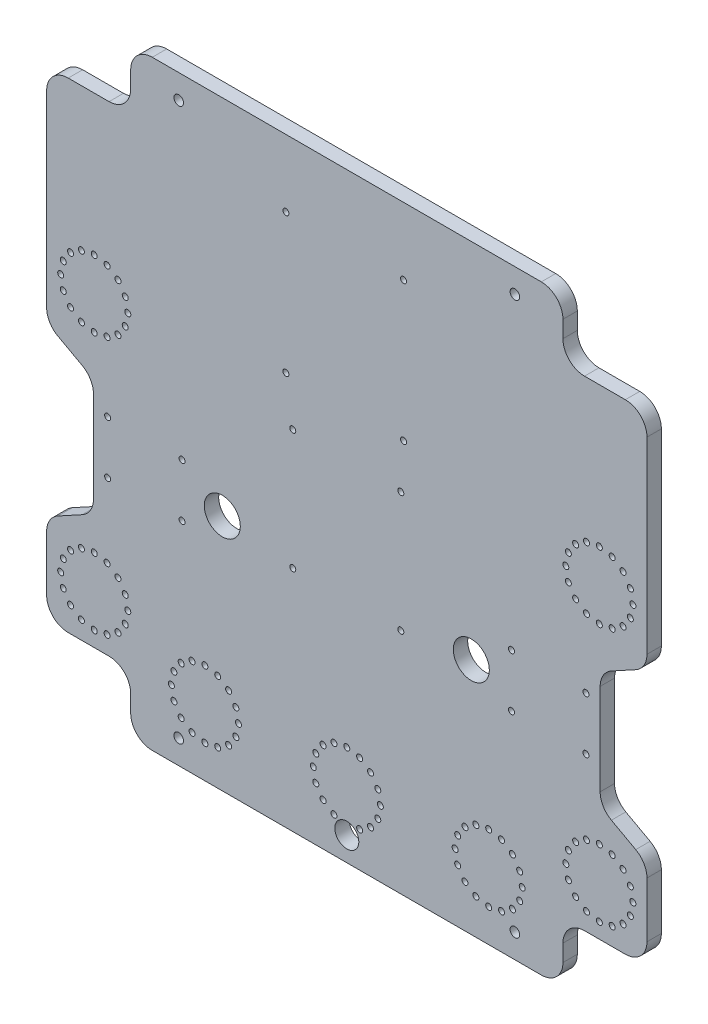
SolidWorks part; units mm, degrees
other "Markup1"
sketch "Sketch7" plane through (25, 0, 0) normal (-0.133, -0.1918, 0.9724) x (0.9904, 0.0125, 0.1379)
material "6061 Alloy"
ref_plane "Front Plane" through (0, 0, 0) normal (0, 0, 1) x (1, 0, 0)
ref_plane "Top Plane" through (0, 0, 0) normal (0, 1, 0) x (1, 0, 0)
ref_plane "Right Plane" through (0, 0, 0) normal (1, 0, 0) x (0, 0, -1)
sketch "Sketch1" plane through (0, 0, 0) normal (0, 0, 1) x (1, 0, 0)
  line L1 (0, 0) -> (300, 0)
  line L2 (0, 0) -> (0, 250)
  line L3 (0, 250) -> (300, 250)
  line L4 (300, 0) -> (300, 250)
  dimension "D1" = 300
  dimension "D2" = 250
extrude "Boss-Extrude1" add sketch "Sketch1" against normal blind 6
sketch "Motor Center Line" plane through (0, 0, -6) normal (0, 0, -1) x (-1, 0, 0)
  line L0 (0, 100) -> (-300, 100) construction
  line L3 (-300, 250) -> (0, 250) construction
  dimension "D1" = 150
sketch "Sketch2" plane through (0, 0, 0) normal (0, 0, 1) x (1, 0, 0)
  line L0 (150, 0.825) -> (150, -0.825) construction
  line L1 (0, 0) -> (20, 0)
  line L2 (0, 0) -> (0, 20)
  line L3 (0, 20) -> (20, 20)
  line L4 (20, 0) -> (20, 20)
  line L5 (300, 20) -> (280, 20)
  line L6 (280, 0) -> (280, 20)
  line L7 (300, 0) -> (280, 0)
  line L8 (300, 0) -> (300, 20)
  line L10 (0, 125) -> (300, 125) construction
  line L11 (0, 250) -> (0, 0) construction
  line L12 (300, 0) -> (300, 250) construction
  line L13 (300, 250) -> (300, 230)
  line L14 (300, 250) -> (280, 250)
  line L15 (280, 250) -> (280, 230)
  line L16 (300, 230) -> (280, 230)
  line L17 (0, 230) -> (20, 230)
  line L18 (20, 250) -> (20, 230)
  line L19 (0, 250) -> (20, 250)
  line L20 (0, 250) -> (0, 230)
  dimension "D1" = 20
sketch "Sketch3" plane through (0, 0, 0) normal (0, 0, 1) x (1, 0, 0)
  line L0 (150, 250) -> (150, 0) construction
  line L1 (0, 0) -> (25, 0)
  line L2 (0, 0) -> (0, 25)
  line L3 (0, 25) -> (25, 25)
  line L4 (25, 0) -> (25, 25)
  line L5 (300, 250) -> (0, 250) construction
  line L6 (0, 0) -> (300, 0) construction
  line L7 (0, 125) -> (300, 125) construction
  line L8 (0, 250) -> (0, 0) construction
  line L9 (300, 0) -> (300, 250) construction
  line L10 (300, 25) -> (275, 25)
  line L11 (275, 0) -> (275, 25)
  line L12 (300, 0) -> (275, 0)
  line L13 (300, 0) -> (300, 25)
  line L14 (300, 250) -> (300, 225)
  line L15 (300, 250) -> (275, 250)
  line L16 (275, 250) -> (275, 225)
  line L17 (300, 225) -> (275, 225)
  line L18 (0, 225) -> (25, 225)
  line L19 (25, 250) -> (25, 225)
  line L20 (0, 250) -> (25, 250)
  line L21 (0, 250) -> (0, 225)
  line L22 (255.5, 73) -> (275, 62.3437)
  line L23 (255.5, 73) -> (255.5, 121.6874)
  line L24 (255.5, 121.6874) -> (275, 132.3437)
  line L25 (275, 132.3437) -> (300, 132.3437)
  line L26 (300, 132.3437) -> (300, 25)
  line L27 (275, 62.3437) -> (275, 25)
  line L28 (44.5, 73) -> (25, 62.3437)
  line L29 (25, 62.3437) -> (25, 25)
  line L30 (44.5, 73) -> (44.5, 121.6874)
  line L31 (265.5, 121.25) -> (265.5, 78.75) construction
  line L32 (44.5, 121.6874) -> (25, 132.3437)
  line L37 (287.5, 132.3437) -> (287.5, 225)
  line L38 (25, 132.3437) -> (0, 132.3437)
  line L39 (12.5, 132.3437) -> (12.5, 225)
  circle A0 centre (201.85, 99.1258) radius 7.5
  circle A1 centre (98.15, 99.1258) radius 7.5
  ellipse E4 centre (201.85, 99.7743) end of major axis (201.2, 99.7743) minor radius 0.6484 construction
  dimension "D3" = 15
  dimension "D1" = 25
  dimension "D2" = 10
  dimension "D4" = 70
extrude "Cut-Extrude1" cut sketch "Sketch3" against normal through all both and the other way through all
sketch "Sketch8" plane through (0, 0, 0) normal (0, 0, 1) x (1, 0, 0)
  circle A0 centre (209.09, 27.66) radius 13.97 construction
  circle A25 centre (209.09, 41.63) radius 1.25
  circle A26 centre (209.09, 13.69) radius 1.25
  circle A27 centre (214.4361, 40.5666) radius 1.25
  circle A28 centre (203.7439, 14.7534) radius 1.25
  circle A29 centre (218.9683, 37.5383) radius 1.25
  circle A30 centre (199.2117, 17.7817) radius 1.25
  circle A31 centre (221.9966, 33.0061) radius 1.25
  circle A32 centre (196.1834, 22.3139) radius 1.25
  circle A33 centre (223.06, 27.66) radius 1.25
  circle A34 centre (195.12, 27.66) radius 1.25
  circle A35 centre (221.9966, 22.3139) radius 1.25
  circle A36 centre (196.1834, 33.0061) radius 1.25
  circle A37 centre (218.9683, 17.7817) radius 1.25
  circle A38 centre (199.2117, 37.5383) radius 1.25
  circle A39 centre (214.4361, 14.7534) radius 1.25
  circle A40 centre (203.7439, 40.5666) radius 1.25
  circle A43 centre (195.12, 27.66) radius 1.6 construction
  circle A44 centre (223.06, 27.66) radius 1.6 construction
  circle A45 centre (90.91, 27.66) radius 13.97 construction
  circle A46 centre (76.94, 27.66) radius 1.25
  circle A47 centre (104.88, 27.66) radius 1.25
  circle A48 centre (76.94, 27.66) radius 1.6 construction
  circle A49 centre (255.1689, 59.2712) radius 1.25
  circle A50 centre (103.8166, 22.3139) radius 1.25
  circle A51 centre (78.0034, 33.0061) radius 1.25
  circle A52 centre (100.7883, 17.7817) radius 1.25
  circle A53 centre (81.0317, 37.5383) radius 1.25
  circle A54 centre (96.2561, 14.7534) radius 1.25
  circle A55 centre (85.5639, 40.5666) radius 1.25
  circle A56 centre (90.91, 13.69) radius 1.25
  circle A57 centre (90.91, 41.63) radius 1.25
  circle A58 centre (85.5639, 14.7534) radius 1.25
  circle A59 centre (96.2561, 40.5666) radius 1.25
  circle A60 centre (81.0317, 17.7817) radius 1.25
  circle A61 centre (100.7883, 37.5383) radius 1.25
  circle A62 centre (78.0034, 22.3139) radius 1.25
  circle A63 centre (103.8166, 33.0061) radius 1.25
  circle A66 centre (104.88, 27.66) radius 1.5 construction
  circle A67 centre (255.1689, 45.3012) radius 13.97 construction
  circle A68 centre (255.1689, 31.3312) radius 1.25
  circle A69 centre (255.1689, 59.2712) radius 1.6 construction
  circle A70 centre (44.8311, 45.3012) radius 13.97 construction
  circle A71 centre (260.515, 58.2078) radius 1.25
  circle A72 centre (249.8228, 32.3946) radius 1.25
  circle A73 centre (265.0472, 55.1795) radius 1.25
  circle A74 centre (245.2907, 35.4229) radius 1.25
  circle A75 centre (268.0755, 50.6473) radius 1.25
  circle A76 centre (242.2623, 39.9551) radius 1.25
  circle A77 centre (269.1389, 45.3012) radius 1.25
  circle A78 centre (241.1989, 45.3012) radius 1.25
  circle A79 centre (268.0755, 39.9551) radius 1.25
  circle A80 centre (242.2623, 50.6473) radius 1.25
  circle A81 centre (265.0472, 35.4229) radius 1.25
  circle A82 centre (245.2907, 55.1795) radius 1.25
  circle A83 centre (260.515, 32.3946) radius 1.25
  circle A84 centre (249.8228, 58.2078) radius 1.25
  circle A87 centre (44.8311, 59.2712) radius 1.25
  circle A88 centre (44.8311, 31.3312) radius 1.25
  circle A89 centre (50.1772, 58.2078) radius 1.25
  circle A90 centre (39.485, 32.3946) radius 1.25
  circle A91 centre (54.7093, 55.1795) radius 1.25
  circle A92 centre (34.9528, 35.4229) radius 1.25
  circle A93 centre (57.7377, 50.6473) radius 1.25
  circle A94 centre (31.9245, 39.9551) radius 1.25
  circle A95 centre (58.8011, 45.3012) radius 1.25
  circle A96 centre (30.8611, 45.3012) radius 1.25
  circle A97 centre (57.7377, 39.9551) radius 1.25
  circle A98 centre (31.9245, 50.6473) radius 1.25
  circle A99 centre (54.7093, 35.4229) radius 1.25
  circle A100 centre (34.9528, 55.1795) radius 1.25
  circle A101 centre (50.1772, 32.3946) radius 1.25
  circle A102 centre (39.485, 58.2078) radius 1.25
  circle A105 centre (44.8311, 31.3312) radius 1.5 construction
  circle A106 centre (44.8311, 59.2712) radius 1.5 construction
  circle A107 centre (255.1689, 152.6711) radius 13.97 construction
  circle A108 centre (255.1689, 166.6411) radius 1.25
  circle A109 centre (255.1689, 138.7011) radius 1.25
  circle A110 centre (249.8228, 139.7645) radius 1.25
  circle A111 centre (260.515, 165.5777) radius 1.25
  circle A112 centre (245.2907, 142.7929) radius 1.25
  circle A113 centre (265.0472, 162.5494) radius 1.25
  circle A114 centre (242.2623, 147.3251) radius 1.25
  circle A115 centre (268.0755, 158.0172) radius 1.25
  circle A116 centre (241.1989, 152.6711) radius 1.25
  circle A117 centre (269.1389, 152.6711) radius 1.25
  circle A118 centre (242.2623, 158.0172) radius 1.25
  circle A119 centre (268.0755, 147.3251) radius 1.25
  circle A120 centre (245.2907, 162.5494) radius 1.25
  circle A121 centre (265.0472, 142.7929) radius 1.25
  circle A122 centre (249.8228, 165.5777) radius 1.25
  circle A123 centre (260.515, 139.7645) radius 1.25
  circle A124 centre (255.1689, 166.6411) radius 1.6 construction
  circle A125 centre (255.1689, 138.7011) radius 1.5 construction
  circle A128 centre (44.8311, 152.6711) radius 13.97 construction
  circle A129 centre (44.8311, 166.6411) radius 1.25
  circle A130 centre (44.8311, 138.7011) radius 1.25
  circle A131 centre (39.485, 139.7645) radius 1.25
  circle A132 centre (50.1772, 165.5777) radius 1.25
  circle A133 centre (34.9528, 142.7929) radius 1.25
  circle A134 centre (54.7093, 162.5494) radius 1.25
  circle A135 centre (31.9245, 147.3251) radius 1.25
  circle A136 centre (57.7377, 158.0172) radius 1.25
  circle A137 centre (30.8611, 152.6711) radius 1.25
  circle A138 centre (58.8011, 152.6711) radius 1.25
  circle A139 centre (31.9245, 158.0172) radius 1.25
  circle A140 centre (57.7377, 147.3251) radius 1.25
  circle A141 centre (34.9528, 162.5494) radius 1.25
  circle A142 centre (54.7093, 142.7929) radius 1.25
  circle A143 centre (39.485, 165.5777) radius 1.25
  circle A144 centre (50.1772, 139.7645) radius 1.25
  circle A147 centre (44.8311, 166.6411) radius 1.6 construction
  circle A148 centre (44.8311, 138.7011) radius 1.6 construction
  circle A149 centre (150, 27.66) radius 13.97 construction
  circle A150 centre (150, 41.63) radius 1.25
  circle A151 centre (150, 13.69) radius 1.25
  circle A152 centre (155.3461, 40.5666) radius 1.25
  circle A153 centre (144.6539, 14.7534) radius 1.25
  circle A154 centre (159.8783, 37.5383) radius 1.25
  circle A155 centre (140.1217, 17.7817) radius 1.25
  circle A156 centre (162.9066, 33.0061) radius 1.25
  circle A157 centre (137.0934, 22.3139) radius 1.25
  circle A158 centre (163.97, 27.66) radius 1.25
  circle A159 centre (136.03, 27.66) radius 1.25
  circle A160 centre (162.9066, 22.3139) radius 1.25
  circle A161 centre (137.0934, 33.0061) radius 1.25
  circle A162 centre (159.8783, 17.7817) radius 1.25
  circle A163 centre (140.1217, 37.5383) radius 1.25
  circle A164 centre (155.3461, 14.7534) radius 1.25
  circle A165 centre (144.6539, 40.5666) radius 1.25
  circle A170 centre (136.03, 27.66) radius 1.6 construction
  circle A171 centre (163.97, 27.66) radius 1.5 construction
  point P40 (209.09, 27.66)
  point P87 (90.91, 27.66)
  point P129 (255.1689, 45.3012)
  point P167 (44.8311, 45.3012)
  point P192 (255.1689, 152.6711)
  point P234 (44.8311, 152.6711)
  point P273 (150, 27.66)
  dimension "D1" = 2.5
  dimension "D2" = 2.5
  dimension "D5" = 2.5
  dimension "D7" = 2.5
  dimension "D9" = 5.4508
  dimension "D10" = 5.3461
  dimension "D11" = 5.3461
  dimension "D12" = 2.5
  dimension "D15" = 2.5
  dimension "D18" = 2.5
  dimension "D20" = 5.4508
  dimension "D14" = 5.4508
  dimension "D17" = 5.4508
  dimension "D3" = 8
  dimension "D4" = 8
  dimension "D6" = 8
  dimension "D8" = 8
  dimension "D13" = 8
  dimension "D16" = 8
  dimension "D19" = 8
sketch "Sketch4" plane through (0, 0, 0) normal (0, 0, 1) x (1, 0, 0)
  arc A0 (174.9953, 164.0221) -> (172.2953, 164.0221) centre (173.6453, 164.0221) ccw construction
  arc A1 (125.9953, 164.0221) -> (123.2953, 164.0221) centre (124.6453, 164.0221) ccw construction
  arc A4 (125.9953, 222.0221) -> (123.2953, 222.0221) centre (124.6453, 222.0221) ccw construction
  arc A5 (174.9953, 222.0221) -> (172.2953, 222.0221) centre (173.6453, 222.0221) ccw construction
  point P23 (127.5, 95)
  point P25 (172.5, 95)
  point P27 (127.5, 145)
  point P29 (172.5, 145)
  point P31 (124.6453, 164.0221)
  point P33 (173.6453, 164.0221)
  point P35 (124.6453, 222.0221)
  point P37 (173.6453, 222.0221)
  point P39 (218.6, 111)
  point P41 (249.6, 111)
  point P43 (249.6, 89)
  point P45 (218.6, 89)
  point P47 (81.4, 89.0063)
  point P49 (50.4, 89.0063)
  point P51 (81.4, 111.0063)
  point P53 (50.4, 111.0063)
extrude "Ultrasonics" cut sketch "Sketch8" against normal through all
sketch "Sketch6" plane through (0, 0, 0) normal (0, 0, 1) x (1, 0, 0)
  line L0 (287.5, 225) -> (275, 225)
  line L1 (275, 0) -> (240, 0)
  line L2 (275, 0) -> (275, 25)
  line L3 (275, 25) -> (240, 25)
  line L4 (240, 0) -> (240, 25)
  line L5 (240, 25) -> (255.5, 73)
  line L6 (150, 250) -> (150, 0) construction
  line L7 (275, 250) -> (25, 250) construction
  line L8 (25, 0) -> (275, 0) construction
  line L9 (60, 25) -> (44.5, 73)
  line L10 (25, 25) -> (60, 25)
  line L11 (60, 0) -> (60, 25)
  line L12 (25, 0) -> (60, 0)
  line L13 (25, 0) -> (25, 25)
  line L14 (275, 250) -> (240, 250)
  line L15 (25, 225) -> (60, 225)
  line L16 (25, 225) -> (25, 250)
  line L17 (25, 250) -> (60, 250)
  line L18 (60, 225) -> (60, 250)
  line L19 (240, 225) -> (240, 250)
  line L20 (275, 225) -> (240, 225)
  line L21 (275, 225) -> (275, 250)
  line L22 (25, 225) -> (25, 132.3437)
  line L23 (275, 132.3437) -> (275, 225)
  line L24 (287.5, 225) -> (287.5, 132.3437)
  line L25 (287.5, 132.3437) -> (275, 132.3437)
  line L26 (25, 225) -> (12.5, 225)
  line L27 (12.5, 225) -> (12.5, 132.3437)
  line L28 (12.5, 132.3437) -> (25, 132.3437)
  dimension "D1" = 25
  dimension "D2" = 35
extrude "Cut-Extrude3" cut sketch "Sketch6" against normal through all
sketch "Sketch5" plane through (0, 0, 0) normal (0, 0, 1) x (1, 0, 0)
  circle A0 centre (50.4, 89.0063) radius 1.25
  dimension "D1" = 2.5
extrude "Cut-Extrude2" cut sketch "Sketch5" against normal through all both
pattern_sketch "Motor Mounts" of "Cut-Extrude2" driven by "Sketch4"
fillet "Fillet1" radius 9 20 edges at (255.5, 121.6874, -3) (44.5, 121.6874, -3) (44.5, 73, -3) (25, 62.3437, -3) (255.5, 73, -3) (275, 62.3437, -3) (240, 250, -3) (240, 225, -3) (60, 250, -3) (60, 225, -3) (60, 0, -3) (240, 0, -3) (275, 225, -3) (275, 132.3437, -3) (25, 225, -3) (25, 132.3437, -3) (60, 25, -3) (25, 25, -3) (275, 25, -3) (240, 25, -3)
sketch "Sketch9" plane through (0, 0, 0) normal (0, 0, 1) x (1, 0, 0)
  line L0 (69, 0) -> (231, 0) construction
  circle A0 centre (150, 10) radius 5
  point P4 (150, 0)
  dimension "D2" = 10
  dimension "D1" = 10
extrude "Limit Switch mount" cut sketch "Sketch9" against normal through all
sketch "Sketch10" plane through (0, 0, 0) normal (0, 0, 1) x (1, 0, 0)
  line L0 (60, 240) -> (240, 240) construction
  line L1 (60, 234) -> (60, 241) construction
  line L2 (240, 234) -> (240, 241) construction
  line L3 (231, 250) -> (69, 250) construction
  line L4 (60, 10) -> (240, 10) construction
  line L5 (60, 9) -> (60, 16) construction
  line L6 (240, 9) -> (240, 16) construction
  line L7 (69, 0) -> (231, 0) construction
  circle A0 centre (80, 240) radius 2
  circle A1 centre (220, 240) radius 2
  circle A2 centre (80, 10) radius 2
  circle A3 centre (220, 10) radius 2
  dimension "D3" = 4
  dimension "D1" = 10
  dimension "D2" = 10
  dimension "D4" = 20
  dimension "D5" = 20
  dimension "D6" = 20
  dimension "D7" = 20
extrude "Aly mount" cut sketch "Sketch10" against normal through all
